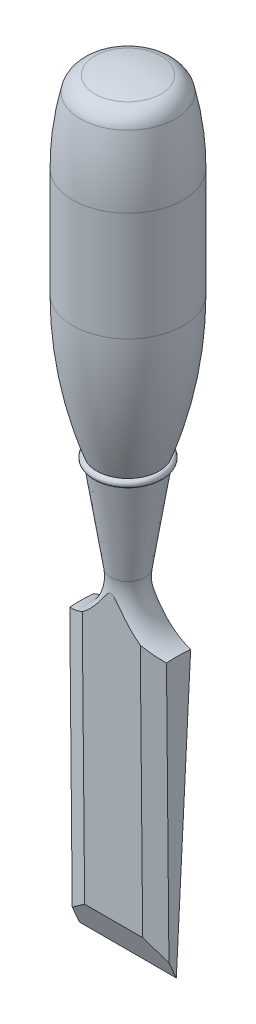
SolidWorks part; units mm, degrees
ref_plane "Front" through (0, 0, 0) normal (0, 0, 1) x (1, 0, 0)
ref_plane "Top" through (0, 0, 0) normal (0, 1, 0) x (1, 0, 0)
ref_plane "Right" through (0, 0, 0) normal (1, 0, 0) x (0, 0, -1)
sketch "Sketch1" plane through (0, 0, 0) normal (0, 0, 1) x (1, 0, 0)
  line L0 (0, 0) -> (0, -30.2482) construction
  line L1 (0, 0) -> (0, 200.025)
  line L2 (0, 0) -> (16.51, 0)
  line L3 (15.9258, 0) -> (-15.9258, 0) construction
  line L4 (16.51, 0) -> (16.51, 72.2343)
  line L5 (14.478, 177.8) -> (14.478, 149.225)
  line L6 (8.1915, 111.125) -> (4.4958, 86.995)
  arc A0 (0, 200.025) -> (8.665, 199.0266) centre (0, 161.925) cw
  arc A1 (14.478, 177.8) -> (12.4548, 195.2425) centre (-61.722, 177.8) ccw
  arc A2 (14.478, 149.225) -> (8.1915, 113.03) centre (-92.863, 149.225) cw
  arc A3 (4.4958, 86.995) -> (16.51, 72.2343) centre (17.1831, 85.0518) ccw
  arc A4 (8.665, 199.0266) -> (12.4548, 195.2425) centre (7.5097, 194.0797) cw
  arc A5 (8.1915, 111.125) -> (8.1915, 113.03) centre (8.1915, 112.0775) ccw
  point P19 (12.7, 73.025)
  dimension "D8" = 38.1
  dimension "D9" = 76.2
  dimension "D13" = 5.08
  dimension "D1" = 200.025
  dimension "D2" = 33.02
  dimension "D3" = 25.4
  dimension "D4" = 28.956
  dimension "D5" = 22.225
  dimension "D6" = 50.8
  dimension "D7" = 88.9
  dimension "D10" = 16.383
  dimension "D11" = 8.9916
  dimension "D12" = 113.03
  dimension "D14" = 73.025
  dimension "D15" = 1.905
revolve "Revolve1" add sketch "Sketch1" angle 360 about L0
sketch "Sketch2" plane through (0, 0, 0) normal (1, 0, 0) x (0, 0, -1)
  line L0 (4.4958, 86.995) -> (0, 0)
  line L1 (0, 0) -> (-3.7569, 8.509)
  line L2 (-3.7569, 8.509) -> (-4.4958, 86.995)
  line L3 (4.4958, 86.995) -> (31.75, 86.995)
  line L4 (27.94, 0) -> (-27.94, 0) construction
  line L5 (-31.75, 86.995) -> (-4.4958, 86.995)
  line L6 (-31.75, 86.995) -> (-31.75, -12.7)
  line L7 (-31.75, -12.7) -> (31.75, -12.7)
  line L8 (31.75, 86.995) -> (31.75, -12.7)
  line L9 (0, 27.94) -> (0, -27.94) construction
  arc A0 (-16.51, 72.2343) -> (-4.4958, 86.995) centre (-17.1831, 85.0518) ccw construction
  point P16 (0, -12.7)
  dimension "D1" = 8.509
  dimension "D2" = 4.191
  dimension "D3" = 63.5
  dimension "D4" = 12.7
extrude "Cut-Extrude1" cut sketch "Sketch2" against normal through all and the other way through all
sketch "Sketch3" plane through (0, 0, 0) normal (0, 0, 1) x (1, 0, 0)
  line L0 (-12.7, -6.35) -> (12.7, -6.35) construction
  line L1 (25.4, 86.995) -> (12.7, 86.995)
  line L2 (25.4, 86.995) -> (25.4, -6.35)
  line L3 (25.4, -6.35) -> (12.7, -6.35)
  line L4 (12.7, 86.995) -> (12.7, -6.35)
  line L5 (-25.4, 86.995) -> (-12.7, 86.995)
  line L6 (-25.4, 86.995) -> (-25.4, -6.35)
  line L7 (-25.4, -6.35) -> (-12.7, -6.35)
  line L8 (-12.7, 86.995) -> (-12.7, -6.35)
  line L9 (0, -27.94) -> (0, 27.94) construction
  line L10 (27.94, 0) -> (-27.94, 0) construction
  line L11 (4.4958, 86.995) -> (0, 86.995) construction
  point P8 (0, -6.35)
  dimension "D1" = 25.4
  dimension "D2" = 6.35
  dimension "D3" = 12.7
extrude "Cut-Extrude2" cut sketch "Sketch3" against normal through all and the other way through all
chamfer "Chamfer1" distance 1.778 distance2 5.08 2 edges at (-12.7, 40.6436, 4.0594) (12.7, 40.6436, 4.0594)
surface "Surface-Offset1" parameters "D1"=6.35
